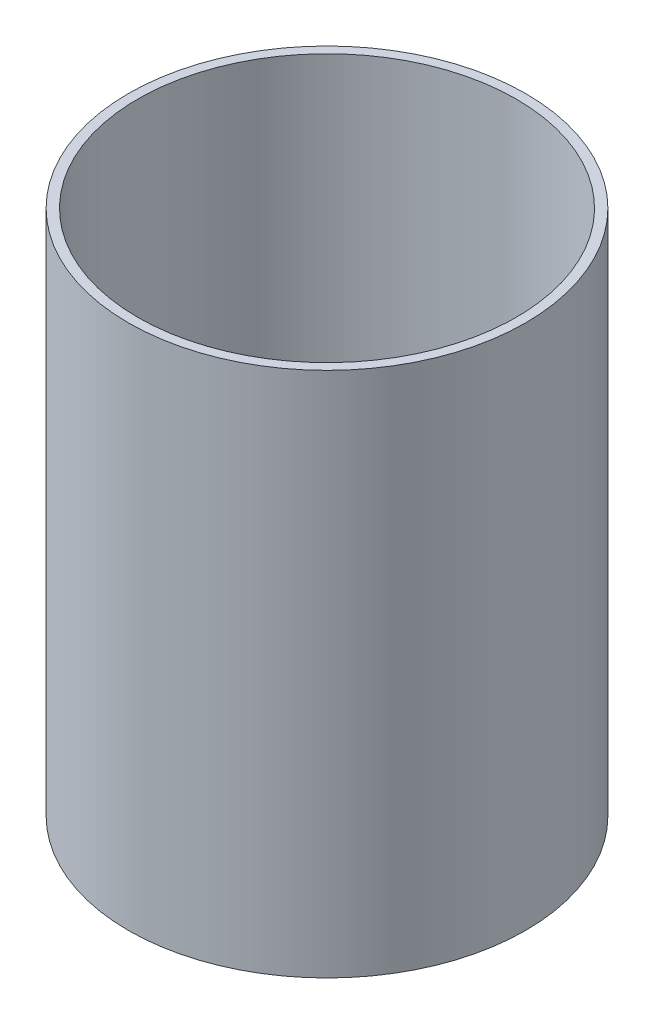
SolidWorks part; units mm, degrees
ref_plane "前视基准面" through (0, 0, 0) normal (0, 0, 1) x (1, 0, 0)
ref_plane "上视基准面" through (0, 0, 0) normal (0, 1, 0) x (1, 0, 0)
ref_plane "右视基准面" through (0, 0, 0) normal (1, 0, 0) x (0, 0, -1)
sketch "草图1" plane through (0, 0, 0) normal (0, 1, 0) x (1, 0, 0)
  circle A0 centre (0, 0) radius 630
  dimension "D1" = 1260
extrude "凸台-拉伸1" add sketch "草图1" along normal blind 1669
sketch "草图2" plane through (0, 1669, 0) normal (0, 1, 0) x (1, 0, 0)
  circle A0 centre (0, 0) radius 600
  dimension "D1" = 1200
extrude "切除-拉伸1" cut sketch "草图2" against normal blind 2914
